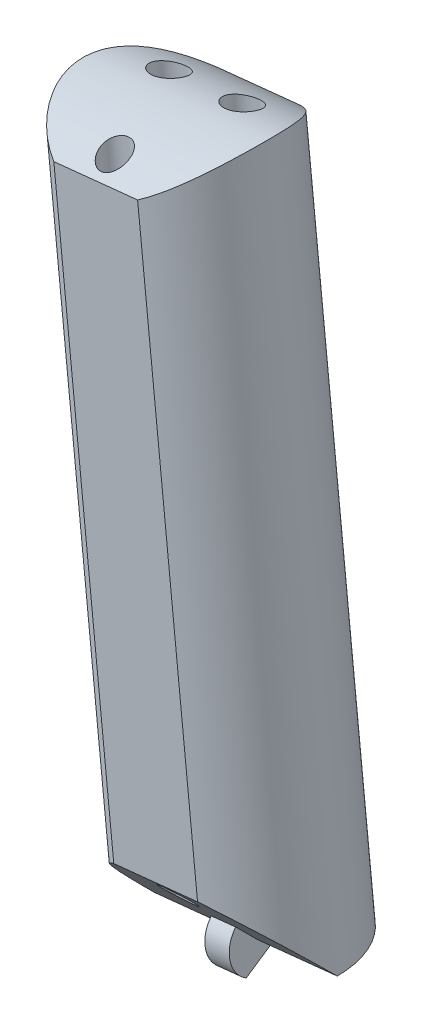
SolidWorks part; units mm, degrees
ref_plane "Front Plane" through (0, 0, 0) normal (0, 0, 1) x (1, 0, 0)
ref_plane "Top Plane" through (0, 0, 0) normal (0, 1, 0) x (1, 0, 0)
ref_plane "Right Plane" through (0, 0, 0) normal (1, 0, 0) x (0, 0, -1)
sketch "Sketch2" plane through (0, 0, 0) normal (0, 0, 1) x (1, 0, 0)
  line L0 (0, 0) -> (90, 0)
  line L1 (90, 0) -> (90, 120)
  line L2 (90, 120) -> (0, 120)
  line L3 (0, 120) -> (0, 0)
  line L4 (0, 120) -> (-10, 120)
  line L5 (-10, 120) -> (-10, 16.9491)
  line L6 (-10, 120) -> (57.5, 127)
  line L7 (57.5, 127) -> (90, 124)
  line L8 (90, 120) -> (99, 60)
  line L10 (90, 124) -> (90, 120)
  line L11 (5.9147, 0) -> (5.9147, -25)
  line L12 (5.9147, -25) -> (-4.0853, -25)
  line L13 (-4.0853, -29) -> (-4.0853, 0)
  line L14 (80, 0) -> (80, -25)
  line L15 (80, -25) -> (90, -25)
  line L16 (90, -29) -> (90, 0)
  line L17 (15.7927, 122.6748) -> (5.4776, 222.1414)
  line L18 (5.4776, 222.1414) -> (21.3923, 223.7918)
  line L19 (21.3923, 223.7918) -> (31.7073, 124.3252)
  line L20 (7.6492, 201.201) -> (23.5639, 202.8514)
  line L21 (10.9066, 169.7905) -> (26.8212, 171.441)
  line L22 (-10, 120) -> (-20.0396, 216.8108)
  line L23 (-20.0396, 216.8108) -> (-4.125, 218.4612)
  line L24 (-4.125, 218.4612) -> (5.9147, 121.6504)
  line L25 (-17.926, 196.4296) -> (-2.0114, 198.08)
  line L26 (-14.7556, 165.8578) -> (1.159, 167.5082)
  line L27 (57.5, 127) -> (46.9095, 229.1223)
  line L28 (46.9095, 229.1223) -> (30.9949, 227.4719)
  line L29 (30.9949, 227.4719) -> (41.5853, 125.3496)
  line L30 (33.2245, 205.9725) -> (49.1391, 207.6229)
  line L31 (36.5688, 173.7233) -> (52.4835, 175.3737)
  line L34 (90, 124) -> (99.1917, 223.5767)
  line L35 (99.1917, 223.5767) -> (83.2594, 225.0473)
  line L36 (83.2594, 225.0473) -> (74.0677, 125.4707)
  line L38 (81.3243, 204.0838) -> (97.2566, 202.6132)
  line L39 (78.4217, 172.6386) -> (94.354, 171.1679)
  line L40 (62.4078, 79.6749) -> (57.5, 127) construction
  line L41 (41.5853, 125.3496) -> (46.4931, 78.0244) construction
  line L42 (46.4931, 78.0244) -> (62.4078, 79.6749) construction
  line L43 (31.7073, 124.3252) -> (36.6151, 77.0001) construction
  line L44 (36.6151, 77.0001) -> (20.7005, 75.3496) construction
  line L45 (20.7005, 75.3496) -> (15.7927, 122.6748) construction
  line L46 (5.9147, 121.6504) -> (10.8224, 74.3253) construction
  line L47 (10.8224, 74.3253) -> (-5.0922, 72.6749) construction
  line L48 (-5.0922, 72.6749) -> (-10, 120) construction
  line L49 (74.0677, 125.4707) -> (69.6944, 78.0931) construction
  line L50 (69.6944, 78.0931) -> (85.7624, 78.0931) construction
  line L51 (85.7624, 78.0931) -> (90, 124) construction
  line L52 (-12.0823, 217.636) -> (10.4873, 0) construction
  line L53 (13.4349, 222.9666) -> (36.5574, 0) construction
  line L54 (38.9522, 228.2971) -> (62.6275, 0) construction
  line L55 (91.2256, 224.312) -> (70.5198, 0) construction
  line L59 (99, 60) -> (93.5277, 44.9649)
  line L60 (99, 60) -> (169.4769, 34.3485)
  line L61 (169.4769, 34.3485) -> (164.0046, 19.3134)
  line L62 (164.0046, 19.3134) -> (93.5277, 44.9649)
  line L63 (90, -2) -> (100, -2)
  line L64 (141.2862, 44.6091) -> (135.8138, 29.574)
  line L65 (99, 60) -> (55.7741, 75.7329) construction
  line L66 (55.7741, 75.7329) -> (50.3018, 60.6978) construction
  line L67 (100, -2) -> (100, -29)
  line L70 (-4.0853, -2) -> (-14.0853, -2)
  line L71 (-14.0853, -2) -> (-14.0853, -29)
  line L74 (-4.0853, 0) -> (0, 0)
  line L75 (-14.0853, -29) -> (-14.0853, -112.587)
  line L76 (-14.0853, -112.587) -> (100, -112.587)
  line L77 (100, -112.587) -> (100, -29)
  line L78 (-14.0853, -29) -> (100, -29)
  line L79 (-14.0853, -14.5) -> (100, -14.5) construction
  line L80 (31.7073, -112.587) -> (31.7073, -122.6232)
  line L81 (31.7073, -122.6232) -> (42.9573, -122.6232)
  line L82 (42.9573, -122.6232) -> (42.9573, -112.587)
  line L83 (-14.0853, -112.587) -> (-88.3667, -112.587)
  line L84 (-88.3667, -112.587) -> (-88.3667, -128.2699)
  line L85 (-88.3667, -128.2699) -> (169.4958, -128.2699)
  line L86 (169.4958, -128.2699) -> (169.4958, -112.587)
  line L87 (169.4958, -112.587) -> (100, -112.587)
  line L88 (90, 60) -> (-10, 60) construction
  line L89 (50.3018, 60.6978) -> (93.5277, 44.9649) construction
  line L90 (87.2806, 55.7521) -> (166.7408, 26.8309) construction
  line L91 (87.2806, 55.7521) -> (82.1749, 52.5336) construction
  line L92 (82.1749, 52.5336) -> (77.3257, 0) construction
  line L93 (83.1185, 56.6957) -> (86.337, 51.59) construction
  arc A0 (-10, 16.9491) -> (-4.0853, 0) centre (14.9876, 16.1624) ccw
  arc A1 (93.5277, 44.9649) -> (90, 0) centre (-126.4069, 39.5988) cw
  point P42 (41.1818, 206.7977)
  point P100 (84.7278, 54.1428)
  point P101 (84.7278, 54.1428)
  dimension "D11" = 47.3684
  dimension "D35" = 9
  dimension "D32" = 220
  dimension "D36" = 25
  dimension "D1" = 120
  dimension "D2" = 90
  dimension "D3" = 10
  dimension "D5" = 67.862
  dimension "D6" = 7
  dimension "D7" = 4
  dimension "D8" = 16
  dimension "D9" = 16
  dimension "D10" = 100
  dimension "D12" = 31.5789
  dimension "D13" = 16
  dimension "D14" = 16
  dimension "D15" = 16
  dimension "D16" = 25.7927
  dimension "D17" = 100
  dimension "D18" = 21.0526
  dimension "D19" = 31.5789
  dimension "D20" = 97.33
  dimension "D21" = 102.67
  dimension "D22" = 20.4905
  dimension "D23" = 30.7358
  dimension "D24" = 21.6147
  dimension "D25" = 32.4221
  dimension "D26" = 25
  dimension "D28" = 25
  dimension "D29" = 75
  dimension "D30" = 47.5789
  dimension "D31" = 30
  dimension "D33" = 46
  dimension "D34" = 20
  dimension "D37" = 2
  dimension "D38" = 2
  dimension "D39" = 27
  dimension "D40" = 10
  dimension "D41" = 10
  dimension "D42" = 27
  dimension "D43" = 14.5
  dimension "D44" = 127.5
ref_plane "Plane1" through (87.2806, 55.7521, 0) normal (-0.846, -0.5333, 0) x (0, 0, 1)
ref_plane "Plane2" through (82.1749, 52.5336, 0) normal (-0.0919, -0.9958, 0) x (-0.9958, 0.0919, 0)
ref_plane "Plane3" through (91.2256, 224.312, 0) normal (-0.0919, -0.9958, 0) x (-0.9958, 0.0919, 0)
ref_plane "Plane4" through (38.9522, 228.2971, 0) normal (0.1032, -0.9947, 0) x (-0.9947, -0.1032, 0)
ref_plane "Plane5" through (13.4349, 222.9666, 0) normal (0.1032, -0.9947, 0) x (-0.9947, -0.1032, 0)
ref_plane "Plane7" through (166.7408, 26.8309, 0) normal (0.9397, -0.342, 0) x (0, 0, -1)
ref_plane "Plane8" through (110.4217, -40.1902, 0) normal (0.9397, -0.342, 0) x (0, 0, -1)
ref_plane "Plane9" through (19.3664, 209.803, 0) normal (-0.0919, -0.9958, 0) x (-0.9958, 0.0919, 0)
ref_plane "Plane10" through (16.4638, 178.3578, 0) normal (-0.0919, -0.9958, 0) x (-0.9958, 0.0919, 0)
ref_plane "Plane11" through (-20.7793, 200.3721, 0) normal (0.1032, -0.9947, 0) x (-0.9947, -0.1032, 0)
ref_plane "Plane12" through (-17.435, 168.1229, 0) normal (0.1032, -0.9947, 0) x (-0.9947, -0.1032, 0)
ref_plane "Plane13" through (-20.5619, 198.2754, 0) normal (0.1032, -0.9947, 0) x (-0.9947, -0.1032, 0)
ref_plane "Plane14" through (-17.3045, 166.8649, 0) normal (0.1032, -0.9947, 0) x (-0.9947, -0.1032, 0)
ref_plane "Plane15" through (-12.0823, 217.636, 0) normal (0.1032, -0.9947, 0) x (-0.9947, -0.1032, 0)
ref_plane "Plane16" through (-20.3445, 196.1788, 0) normal (0.1032, -0.9947, 0) x (-0.9947, -0.1032, 0)
ref_plane "Plane17" through (-17.1741, 165.607, 0) normal (0.1032, -0.9947, 0) x (-0.9947, -0.1032, 0)
ref_plane "Plane18" through (12.1098, 131.1899, 0) normal (-0.0919, -0.9958, 0) x (-0.9958, 0.0919, 0)
ref_plane "Plane19" through (-12.4184, 119.7492, 0) normal (0.1032, -0.9947, 0) x (-0.9947, -0.1032, 0)
ref_plane "Plane20" through (0, 0, 0) normal (0, 0, 1) x (0.1032, -0.9947, 0)
ref_plane "Plane21" through (0, 0, 0) normal (0, 0, 1) x (-0.0919, -0.9958, 0)
ref_plane "Plane22" through (10.3758, 1.076, 0) normal (-0.9947, -0.1032, 0) x (0.1032, -0.9947, 0)
ref_plane "Plane23" through (36.1684, 3.7508, 0) normal (-0.9947, -0.1032, 0) x (0.1032, -0.9947, 0)
ref_plane "Plane24" through (61.9611, 6.4256, 0) normal (-0.9947, -0.1032, 0) x (0.1032, -0.9947, 0)
ref_plane "Plane25" through (69.924, -6.4545, 0) normal (-0.9958, 0.0919, 0) x (-0.0919, -0.9958, 0)
sketch "Sketch3" plane through (-12.0823, 217.636, 0) normal (0.1032, -0.9947, 0) x (-0.9947, -0.1032, 0)
  circle A0 centre (0, 0) radius 9
  dimension "D1" = 18
extrude "Boss-Extrude1" add sketch "Sketch3" along normal blind 69
sketch "Sketch4" plane through (10.3758, 1.076, 0) normal (-0.9947, -0.1032, 0) x (0.1032, -0.9947, 0)
  line L0 (-217.7214, 9) -> (-212.7214, 9)
  line L1 (-148.7214, 9) -> (-217.7214, 9) construction
  line L2 (-217.7214, 9) -> (-217.7214, -9)
  line L3 (-217.7214, -9) -> (-212.7214, -9)
  line L4 (-217.7214, -9) -> (-148.7214, -9) construction
  arc A1 (-212.7214, 9) -> (-212.7214, -9) centre (-203.5065, 0) ccw
  dimension "D1" = 5
extrude "Cut-Extrude1" cut sketch "Sketch4" against normal through all and the other way through all
sketch "Sketch5" plane through (10.3758, 1.076, 0) normal (-0.9947, -0.1032, 0) x (0.1032, -0.9947, 0)
  line L0 (-148.7214, 0) -> (-157.7214, 9)
  line L1 (-148.7214, -9) -> (-148.7214, 9) construction
  line L2 (-148.7214, 9) -> (-212.7214, 9) construction
  line L3 (-157.7214, 9) -> (-148.7214, 9)
  line L4 (-148.7214, 9) -> (-148.7214, 0)
  dimension "D1" = 45
extrude "Cut-Extrude2" cut sketch "Sketch5" against normal through all and the other way through all
sketch "Sketch7" plane through (10.3758, 1.076, 0) normal (-0.9947, -0.1032, 0) x (0.1032, -0.9947, 0)
  line L5 (-151.5191, 0.1122) -> (-148.7214, 0)
  line L11 (-148.7214, 0) -> (-148.7214, -2.8)
  line L12 (-148.7214, -9) -> (-148.7214, 0) construction
  line L15 (-148.7214, -2.8) -> (-146.2965, 1.4)
  arc A0 (-151.5191, 0.1122) -> (-146.2965, 1.4) centre (-148.7214, 0) cw
  dimension "D2" = 30
  dimension "D1" = 2.8
  dimension "D3" = 2.8
extrude "Boss-Extrude3" add sketch "Sketch7" along normal mid plane 2.4
sketch "Sketch8" plane through (-12.0823, 217.636, 0) normal (0.1032, -0.9947, 0) x (-0.9947, -0.1032, 0)
  line L0 (8, 0) -> (-8, 0) construction
  circle A0 centre (-3.6, 3) radius 1.6
  circle A1 centre (3.6, 3) radius 1.6
  circle A3 centre (0, -6) radius 1.4
  point P6 (0, 0)
  dimension "D1" = 3.2
  dimension "D2" = 3.2
  dimension "D7" = 2.8
  dimension "D3" = 3
  dimension "D4" = 3
  dimension "D5" = 3.6
  dimension "D6" = 3.6
  dimension "D8" = 6
extrude "Cut-Extrude3" cut sketch "Sketch8" against normal through all and the other way through all
sketch "Sketch9" plane through (-15.3407, 147.9281, 0) normal (0.1032, -0.9947, 0) x (0.9947, 0.1032, 0)
  line L0 (6.3083, -8) -> (14.5545, -8)
  line L1 (6.3083, 8) -> (14.5545, 8)
  line L2 (2.4314, 0) -> (18.4314, 0) construction
  arc A0 (1.4314, 0) -> (19.4314, 0) centre (10.4314, 0) ccw construction
  arc A1 (6.3083, -8) -> (14.5545, -8) centre (10.4314, 0) ccw
  arc A2 (19.4314, 0) -> (1.4314, 0) centre (10.4314, 0) ccw construction
  arc A3 (6.3083, 8) -> (14.5545, 8) centre (10.4314, 0) cw
  dimension "D1" = 8
  dimension "D2" = 8
extrude "Cut-Extrude4" cut sketch "Sketch9" against normal through all
